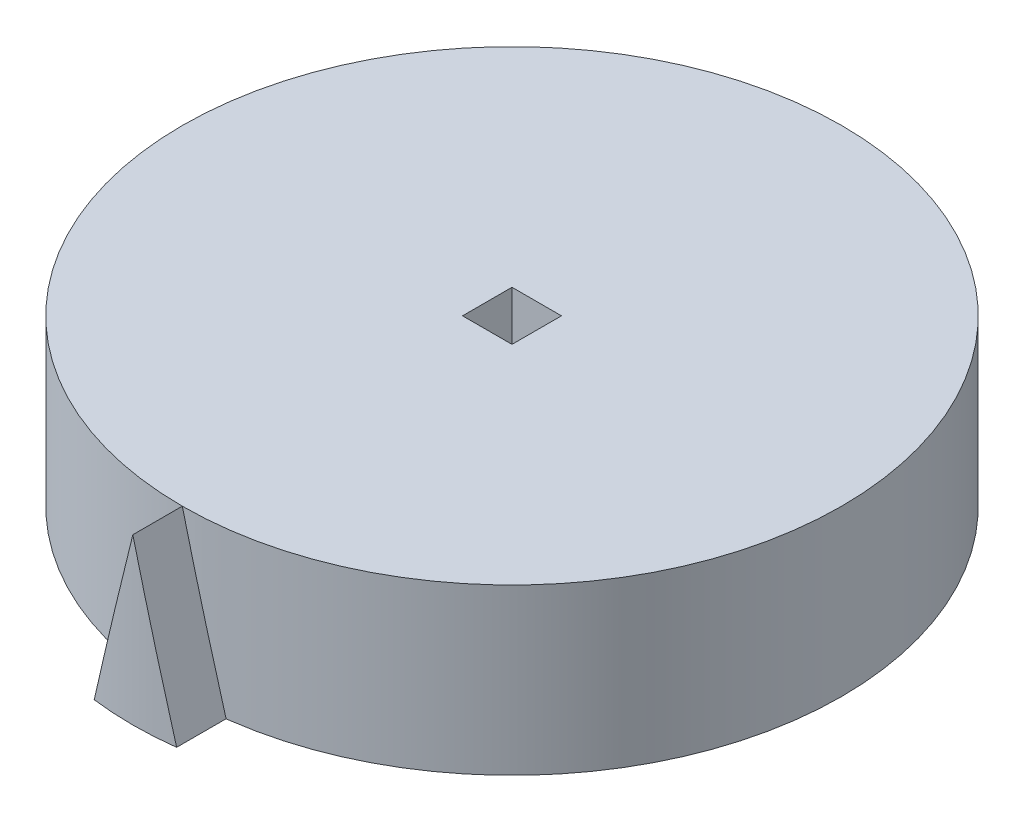
SolidWorks part; units mm, degrees
ref_plane "Front Plane" through (0, 0, 0) normal (0, 0, 1) x (1, 0, 0)
ref_plane "Top Plane" through (0, 0, 0) normal (0, 1, 0) x (1, 0, 0)
ref_plane "Right Plane" through (0, 0, 0) normal (1, 0, 0) x (0, 0, -1)
sketch "Sketch1" plane through (0, 0, 0) normal (0, 1, 0) x (1, 0, 0)
  line L1 (-1.5, 1.5) -> (1.5, 1.5)
  line L2 (-1.5, 1.5) -> (-1.5, -1.5)
  line L3 (-1.5, -1.5) -> (1.5, -1.5)
  line L4 (1.5, 1.5) -> (1.5, -1.5)
  circle A0 centre (0, 0) radius 20
  dimension "D1" = 3
  dimension "D2" = 3
  dimension "D3" = 1.5
  dimension "D4" = 1.5
extrude "Boss-Extrude1" add sketch "Sketch1" along normal blind 10
sketch "Sketch2" plane through (0, 0, 0) normal (0, 0, 1) x (1, 0, 0)
  line L0 (0, 10) -> (-2.5, 0.0018)
  line L1 (-1.5, 10) -> (1.5, 10) construction
  line L2 (-2.5, 0.0018) -> (2.5, 0.0018)
  line L3 (2.5, 0.0018) -> (0, 10)
  dimension "D1" = 5
  dimension "D2" = 2.5
extrude "Boss-Extrude2" add sketch "Sketch2" along normal blind 3 from surface starting at face at (0, 10, 20)
